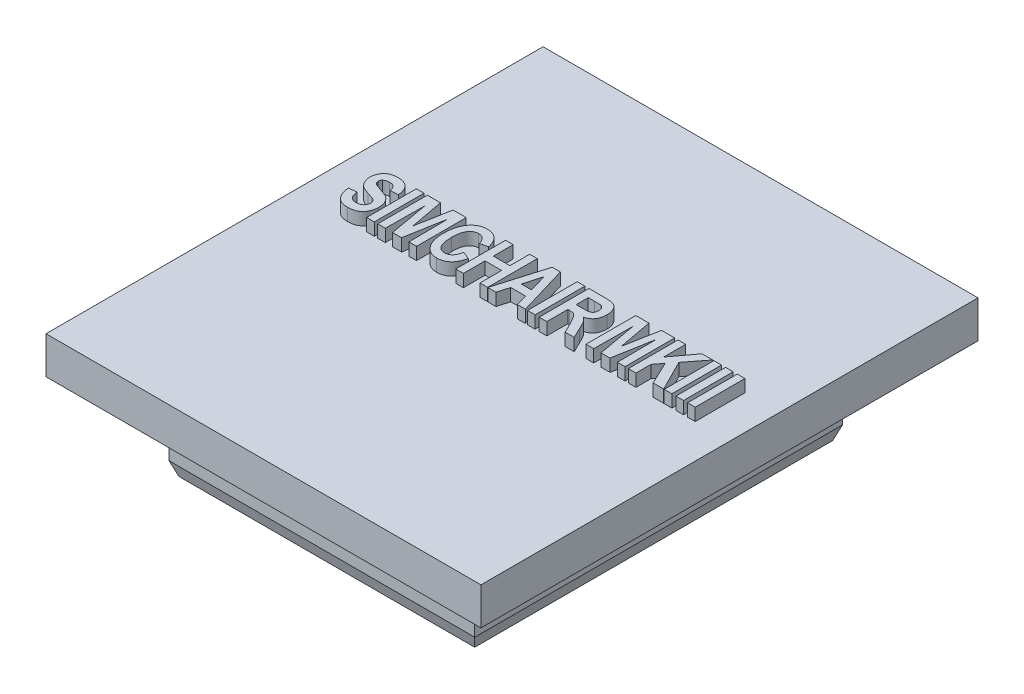
SolidWorks part; units mm, degrees
ref_plane "Спереди" through (0, 0, 0) normal (0, 0, 1) x (1, 0, 0)
ref_plane "Сверху" through (0, 0, 0) normal (0, 1, 0) x (1, 0, 0)
ref_plane "Справа" through (0, 0, 0) normal (1, 0, 0) x (0, 0, -1)
sketch "Sketch1" plane through (0, 0, 0) normal (0, 1, 0) x (1, 0, 0)
  line L1 (12.3, -14.8) -> (-12.3, -14.8)
  line L2 (12.3, -14.8) -> (12.3, 14.8)
  line L3 (12.3, 14.8) -> (-12.3, 14.8)
  line L4 (-12.3, -14.8) -> (-12.3, 14.8)
  line L5 (12.3, -14.8) -> (-12.3, 14.8) construction
  line L6 (12.3, 14.8) -> (-12.3, -14.8) construction
  point P0 (0, 0)
  dimension "D1" = 24.6
  dimension "D2" = 29.6
extrude "Boss-Extrude1" add sketch "Sketch1" along normal blind 4
sketch "Sketch2" plane through (0, 4, 0) normal (0, 1, 0) x (1, 0, 0)
  line L0 (-2.7, 14.8) -> (-2.7, -14.8) construction
  line L1 (12.3, 14.8) -> (-12.3, 14.8) construction
  line L2 (-12.3, -14.8) -> (12.3, -14.8) construction
  line L3 (-12.3, 3.2) -> (12.3, 3.2) construction
  line L4 (-12.3, 14.8) -> (-12.3, -14.8) construction
  line L5 (12.3, -14.8) -> (12.3, 14.8) construction
  line L7 (14.8, -16.8) -> (-20.2, -16.8)
  line L8 (14.8, -16.8) -> (14.8, 23.2)
  line L9 (14.8, 23.2) -> (-20.2, 23.2)
  line L10 (-20.2, -16.8) -> (-20.2, 23.2)
  line L11 (14.8, -16.8) -> (-20.2, 23.2) construction
  line L12 (14.8, 23.2) -> (-20.2, -16.8) construction
  point P12 (-2.7, 3.2)
  dimension "D1" = 35
  dimension "D2" = 40
  dimension "D3" = 18
  dimension "D4" = 15
extrude "Boss-Extrude2" add sketch "Sketch2" along normal blind 3
chamfer "Chamfer1" distance 0.4 angle 70 4 edges at (0, 0, 14.8) (12.3, 0, 0) (0, 0, -14.8) (-12.3, 0, 0)
sketch "Sketch3" plane through (0, 7, 0) normal (0, 1, 0) x (1, 0, 0)
  line L0 (-20.2, 3.2) -> (14.8, 3.2) construction
  line L1 (-20.2, 23.2) -> (-20.2, -16.8) construction
  line L2 (14.8, -16.8) -> (14.8, 23.2) construction
  text T0 "<b>SIMCHAIR MKIII</b>" font "Arial" height 4
  point P9 (0, 0)
  point P10 (-20.2, 3.2)
extrude "Boss-Extrude3" add sketch "Sketch3" along normal blind 1
